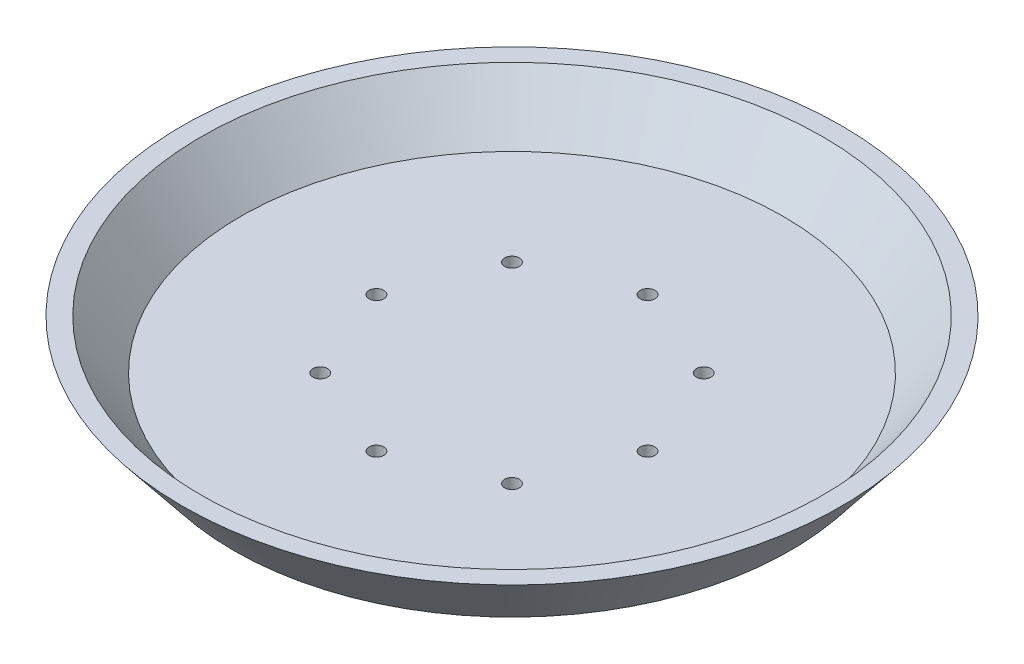
SolidWorks part; units mm, degrees
ref_plane "Front Plane" through (0, 0, 0) normal (0, 0, 1) x (1, 0, 0)
ref_plane "Top Plane" through (0, 0, 0) normal (0, 1, 0) x (1, 0, 0)
ref_plane "Right Plane" through (0, 0, 0) normal (1, 0, 0) x (0, 0, -1)
sketch "Sketch1" plane through (0, 0, 0) normal (0, 0, 1) x (1, 0, 0)
  line L0 (55, 0) -> (63, 10)
  line L1 (63, 10) -> (66.8419, 10)
  line L3 (56.4419, -3) -> (0, -3)
  line L4 (0, -3) -> (0, 0)
  line L5 (0, 0) -> (55, 0)
  line L6 (66.8419, 10) -> (56.4419, -3)
  dimension "D1" = 55
  dimension "D2" = 8
  dimension "D3" = 10
  dimension "D4" = 3
  dimension "D6" = 3
revolve "Revolve1" add sketch "Sketch1" angle 360 about L4
sketch "Sketch2" plane through (0, -3, 0) normal (0, -1, 0) x (-1, 0, 0)
  circle A0 centre (0, -27.5) radius 1.5
  circle A1 centre (-19.4454, -19.4454) radius 1.5
  circle A2 centre (-27.5, 0) radius 1.5
  circle A3 centre (-19.4454, 19.4454) radius 1.5
  circle A4 centre (0, 27.5) radius 1.5
  circle A5 centre (19.4454, 19.4454) radius 1.5
  circle A6 centre (27.5, 0) radius 1.5
  circle A7 centre (19.4454, -19.4454) radius 1.5
  point P20 (0, 0)
  dimension "D2" = 3
  dimension "D1" = 27.5
  dimension "D3" = 8
extrude "Cut-Extrude1" cut sketch "Sketch2" against normal through all
